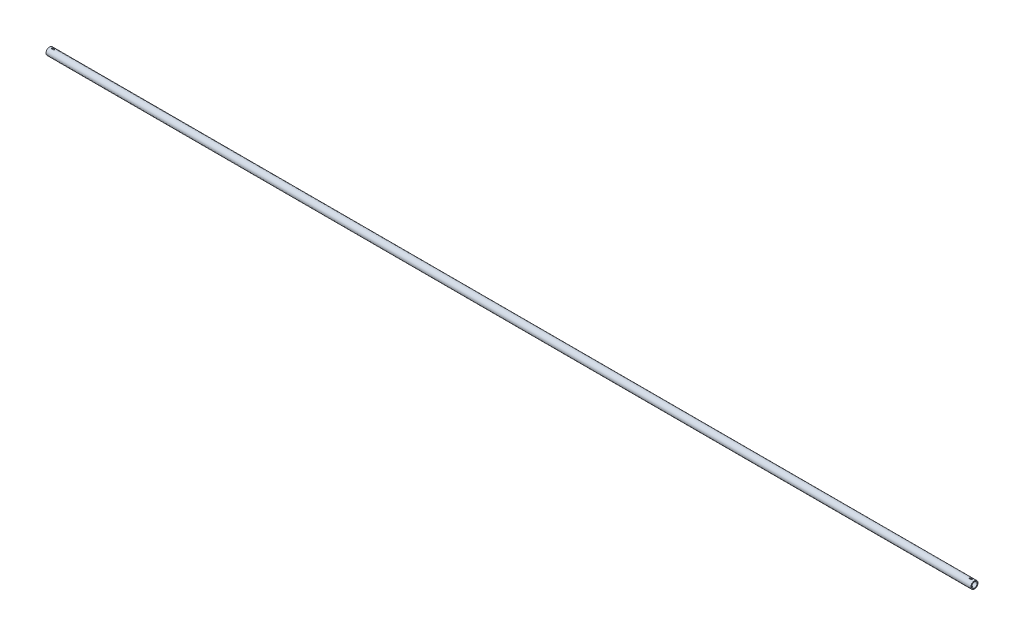
SolidWorks part; units mm, degrees
material "AISI 1045 钢，冷拔"
ref_plane "前视基准面" through (0, 0, 0) normal (0, 0, 1) x (1, 0, 0)
ref_plane "上视基准面" through (0, 0, 0) normal (0, 1, 0) x (1, 0, 0)
ref_plane "右视基准面" through (0, 0, 0) normal (1, 0, 0) x (0, 0, -1)
sketch "草图1" plane through (0, 0, 0) normal (1, 0, 0) x (0, 0, -1)
  circle A0 centre (0, 0) radius 20
  circle A2 centre (0, 0) radius 14
  dimension "D1" = 6
  dimension "D2" = 40
extrude "凸台-拉伸1" add sketch "草图1" along normal blind 5145
sketch "草图2" plane through (0, 0, 0) normal (-1, 0, 0) x (0, 0, 1)
  circle A0 centre (0, 0) radius 15
  dimension "D1" = 30
extrude "切除-拉伸1" cut sketch "草图2" against normal blind 70
sketch "草图3" plane through (5145, 0, 0) normal (1, 0, 0) x (0, 0, -1)
  circle A0 centre (0, 0) radius 15
  dimension "D1" = 30
extrude "切除-拉伸2" cut sketch "草图3" against normal blind 70
sketch "草图4" plane through (0, 0, 0) normal (0, 1, 0) x (1, 0, 0)
  line L0 (10.164, 0) -> (5163.2865, 0) construction
  line L1 (5145, -20) -> (5145, 20) construction
  line L2 (5120, 3) -> (5130, 3)
  line L3 (5120, -3) -> (5130, -3)
  line L4 (0, 20) -> (0, -20) construction
  line L5 (15, 3) -> (25, 3)
  line L6 (15, -3) -> (25, -3)
  arc A0 (5130, -3) -> (5130, 3) centre (5130, 0) ccw
  arc A1 (5120, 3) -> (5120, -3) centre (5120, 0) ccw
  arc A2 (15, 3) -> (15, -3) centre (15, 0) ccw
  arc A3 (25, -3) -> (25, 3) centre (25, 0) ccw
  dimension "D1" = 6
  dimension "D3" = 25
  dimension "D4" = 6
  dimension "D5" = 6
  dimension "D6" = 15
  dimension "D8" = 6
  dimension "D9" = 6
  dimension "D2" = 15
  dimension "D7" = 25
  dimension "D10" = 6
extrude "切除-拉伸3" cut sketch "草图4" against normal through all both and the other way through all
